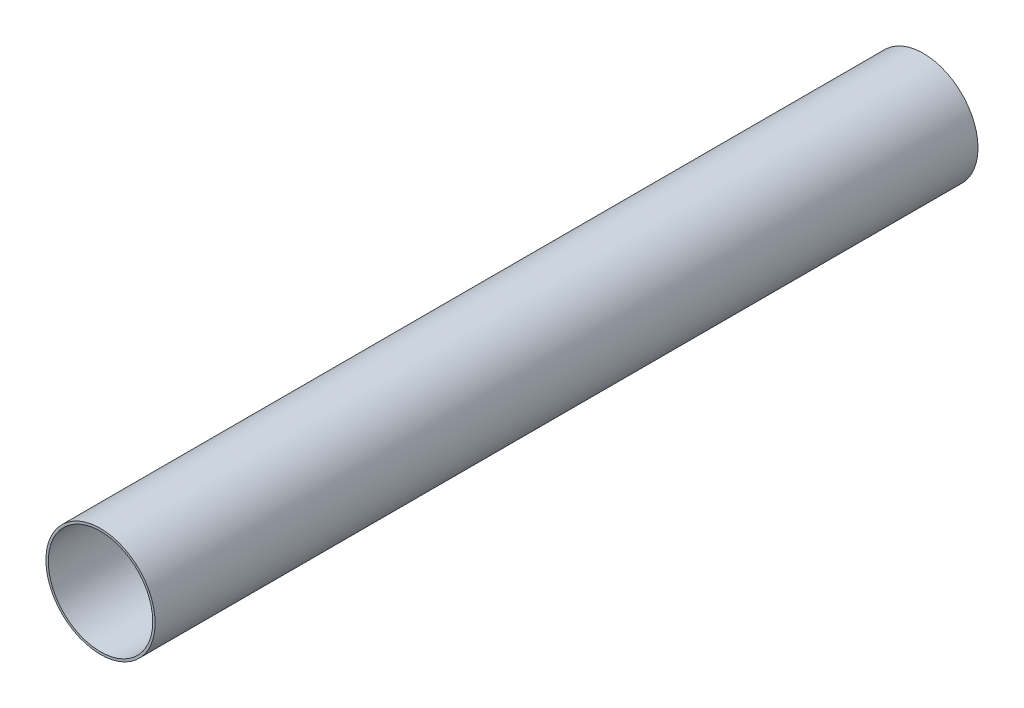
SolidWorks part; units mm, degrees
material "Hexcel AS4C (3000 Filaments)"
ref_plane "Front Plane" through (0, 0, 0) normal (0, 0, 1) x (1, 0, 0)
ref_plane "Top Plane" through (0, 0, 0) normal (0, 1, 0) x (1, 0, 0)
ref_plane "Right Plane" through (0, 0, 0) normal (1, 0, 0) x (0, 0, -1)
sketch "Sketch1" plane through (0, 0, 0) normal (0, 0, 1) x (1, 0, 0)
  circle A0 centre (0, 0) radius 25.4
  circle A1 centre (0, 0) radius 26.545
  dimension "D1" = 50.8
  dimension "D2" = 53.09
extrude "Boss-Extrude1" add sketch "Sketch1" along normal blind 400
